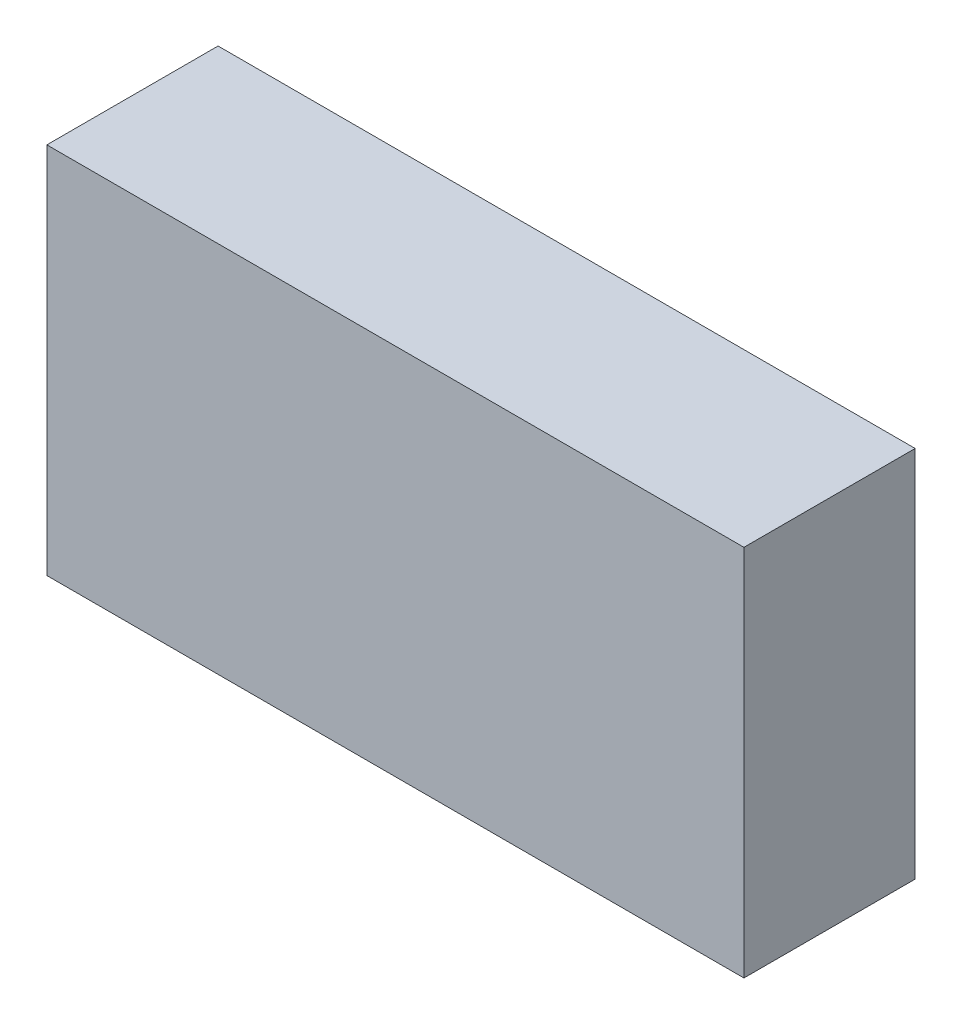
SolidWorks part; units mm, degrees
ref_plane "Front Plane" through (0, 0, 0) normal (0, 0, 1) x (1, 0, 0)
ref_plane "Top Plane" through (0, 0, 0) normal (0, 1, 0) x (1, 0, 0)
ref_plane "Right Plane" through (0, 0, 0) normal (1, 0, 0) x (0, 0, -1)
sketch "Sketch1" plane through (0, 0, 0) normal (0, 0, 1) x (1, 0, 0)
  line L1 (28.5, -15.25) -> (-28.5, -15.25)
  line L2 (28.5, -15.25) -> (28.5, 15.25)
  line L3 (28.5, 15.25) -> (-28.5, 15.25)
  line L4 (-28.5, -15.25) -> (-28.5, 15.25)
  line L5 (28.5, -15.25) -> (-28.5, 15.25) construction
  line L6 (28.5, 15.25) -> (-28.5, -15.25) construction
  point P0 (0, 0)
  dimension "D1" = 57
  dimension "D2" = 30.5
extrude "Boss-Extrude1" add sketch "Sketch1" along normal blind 14
